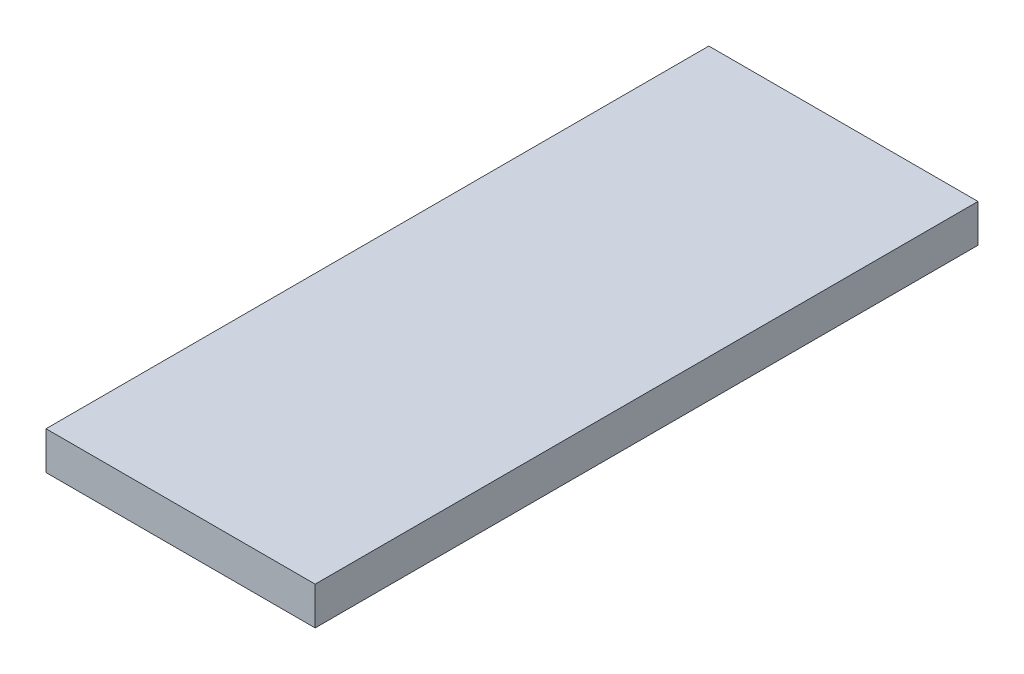
SolidWorks part; units mm, degrees
ref_plane "Front Plane" through (0, 0, 0) normal (0, 0, 1) x (1, 0, 0)
ref_plane "Top Plane" through (0, 0, 0) normal (0, 1, 0) x (1, 0, 0)
ref_plane "Right Plane" through (0, 0, 0) normal (1, 0, 0) x (0, 0, -1)
sketch "Sketch1" plane through (0, 0, 0) normal (0, 1, 0) x (1, 0, 0)
  line L1 (0, 0) -> (18.0086, 0)
  line L2 (0, 0) -> (0, 44.3484)
  line L3 (0, 44.3484) -> (18.0086, 44.3484)
  line L4 (18.0086, 0) -> (18.0086, 44.3484)
  dimension "D1" = 44.3484
  dimension "D2" = 18.0086
extrude "Boss-Extrude1" add sketch "Sketch1" along normal blind 2.54
